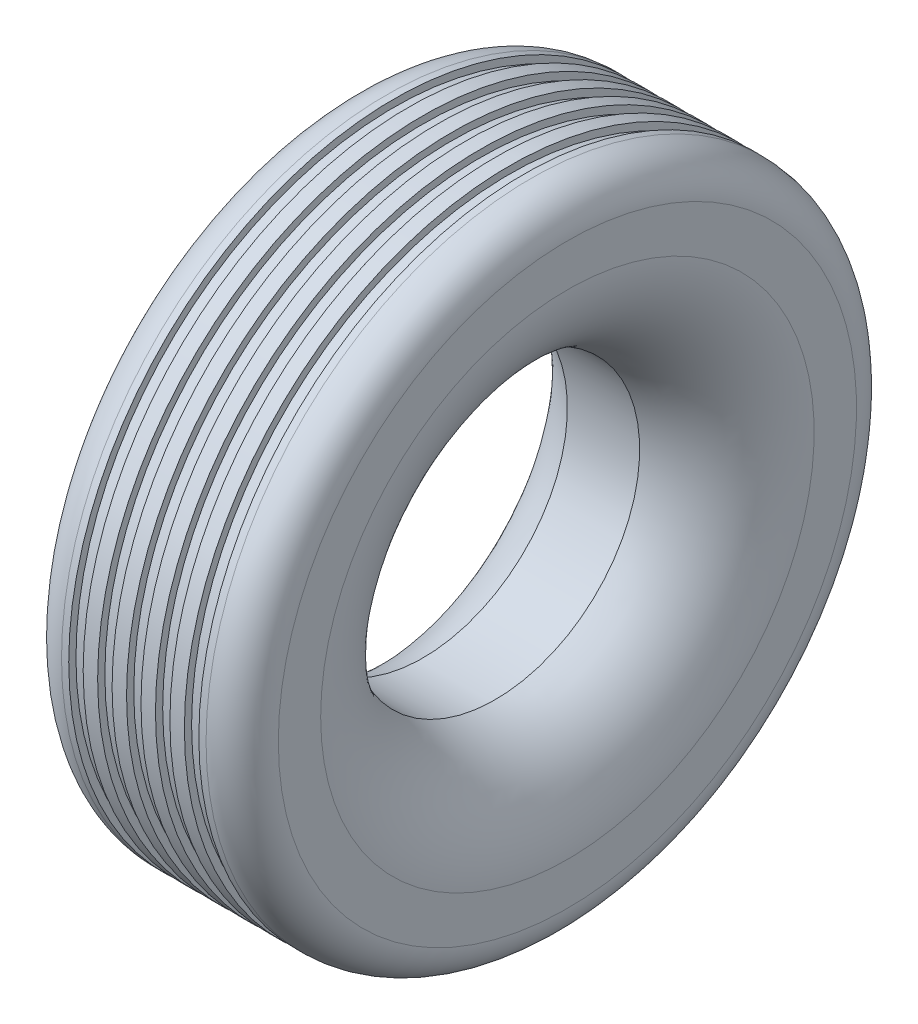
SolidWorks part; units mm, degrees
ref_plane "Front Plane" through (0, 0, 0) normal (0, 0, 1) x (1, 0, 0)
ref_plane "Top Plane" through (0, 0, 0) normal (0, 1, 0) x (1, 0, 0)
ref_plane "Right Plane" through (0, 0, 0) normal (1, 0, 0) x (0, 0, -1)
sketch "Sketch2" plane through (0, 0, 0) normal (0, 0, 1) x (1, 0, 0)
  line L10 (60, 450) -> (60, 440)
  line L15 (0, 0) -> (100, 0) construction
  line L16 (0, 341.4214) -> (0, 400)
  line L17 (50, 450) -> (60, 450)
  line L18 (300, 341.4214) -> (300, 400)
  line L19 (60, 440) -> (80, 440)
  line L20 (80, 440) -> (80, 450)
  line L21 (100, 450) -> (100, 440)
  line L22 (100, 440) -> (120, 440)
  line L23 (120, 440) -> (120, 450)
  line L24 (140, 450) -> (140, 440)
  line L25 (140, 440) -> (160, 440)
  line L26 (160, 440) -> (160, 450)
  line L27 (180, 450) -> (180, 440)
  line L28 (180, 440) -> (200, 440)
  line L29 (200, 440) -> (200, 450)
  line L30 (220, 450) -> (220, 440)
  line L31 (220, 440) -> (240, 440)
  line L32 (240, 440) -> (240, 450)
  line L33 (240, 450) -> (250, 450)
  line L34 (200, 450) -> (220, 450)
  line L35 (160, 450) -> (180, 450)
  line L36 (120, 450) -> (140, 450)
  line L37 (80, 450) -> (100, 450)
  line L38 (100, 0) -> (100, 200)
  line L39 (150, 0) -> (150, 291.5076) construction
  line L40 (200, 0) -> (200, 200)
  line L41 (100, 0) -> (200, 0)
  arc A13 (250, 450) -> (300, 400) centre (250, 400) cw
  arc A14 (0, 400) -> (50, 450) centre (50, 400) cw
  arc A15 (0, 341.4214) -> (100, 200) centre (150, 341.4214) ccw
  arc A16 (300, 341.4214) -> (200, 200) centre (150, 341.4214) cw
  point P11 (300, 450)
  dimension "D1" = 450
  dimension "D3" = 50
  dimension "D4" = 10
  dimension "D7" = 10
  dimension "D6" = 20
  dimension "D5" = 20
  dimension "D8" = 200
revolve "Revolve2" add sketch "Sketch2" angle 360 about L41
sketch "Sketch5" plane through (100, 0, 0) normal (-1, 0, 0) x (0, 0, 1)
  circle A0 centre (0, 0) radius 200
  dimension "D1" = 400
extrude "Cut-Extrude3" cut sketch "Sketch5" against normal through all
